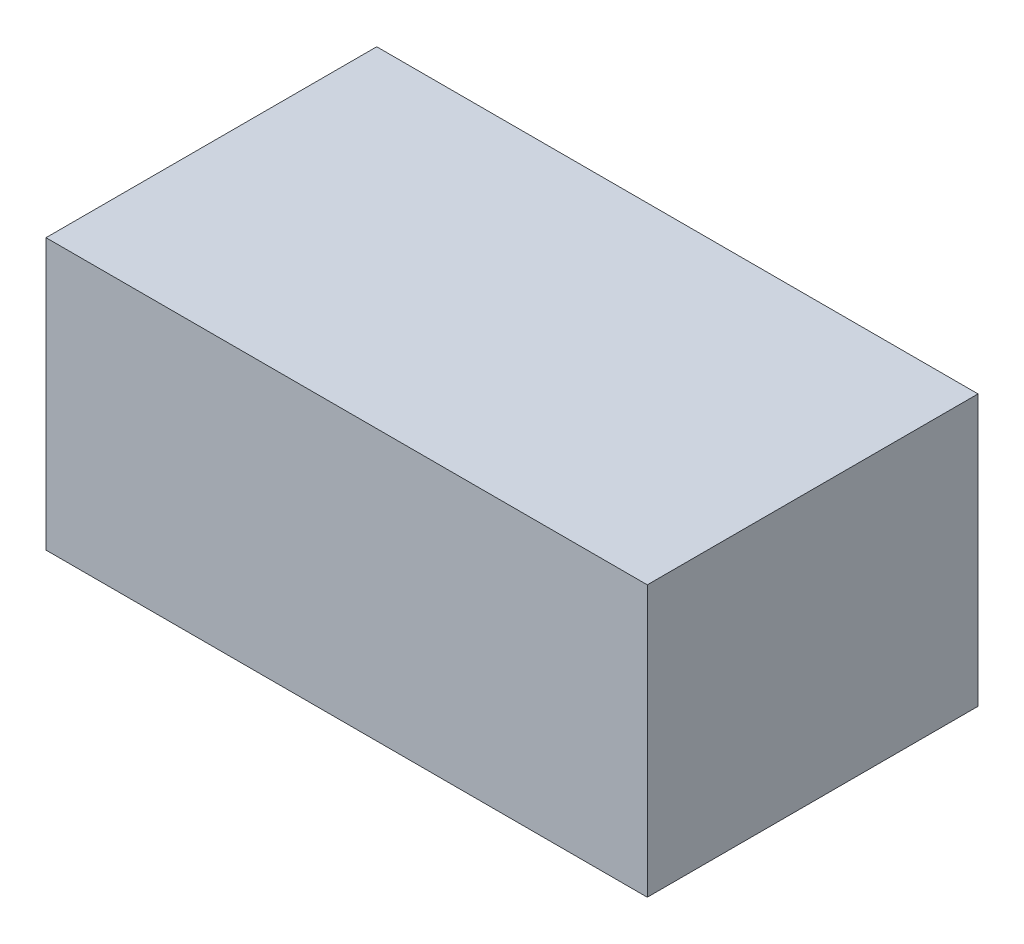
SolidWorks part; units mm, degrees
ref_plane "Plan de face" through (0, 0, 0) normal (0, 0, 1) x (1, 0, 0)
ref_plane "Plan de dessus" through (0, 0, 0) normal (0, 1, 0) x (1, 0, 0)
ref_plane "Plan de droite" through (0, 0, 0) normal (1, 0, 0) x (0, 0, -1)
sketch "Esquisse1" plane through (0, 0, 0) normal (0, 0, 1) x (1, 0, 0)
  line L1 (0, 0) -> (100, 0)
  line L2 (0, 0) -> (0, 45)
  line L3 (0, 45) -> (100, 45)
  line L4 (100, 0) -> (100, 45)
  dimension "D1" = 100
  dimension "D2" = 45
extrude "Boss.-Extru.1" add sketch "Esquisse1" along normal blind 55
